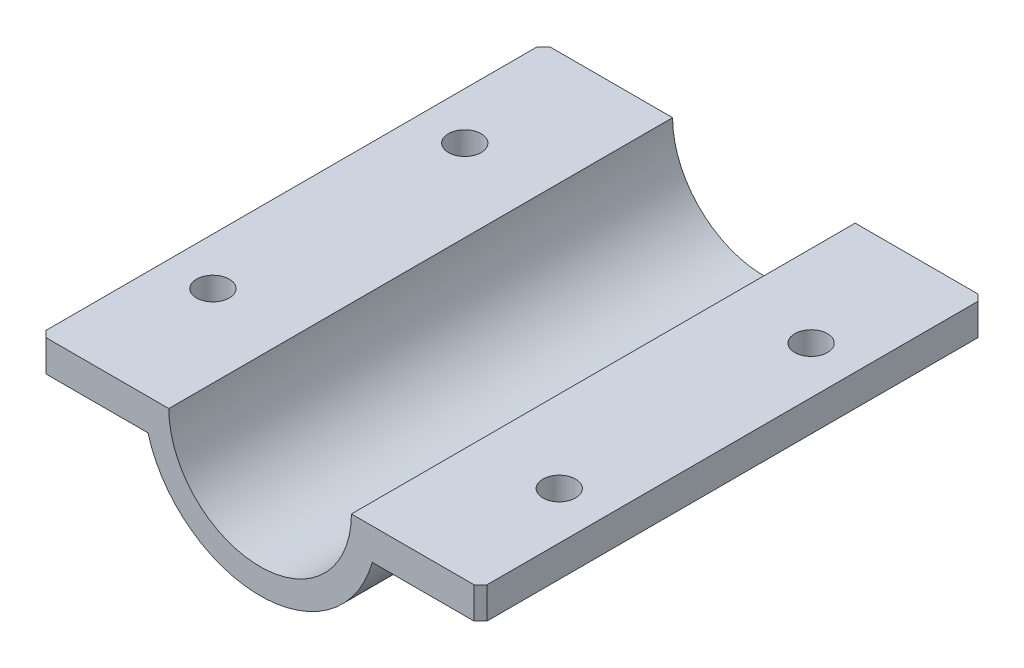
SolidWorks part; units mm, degrees
ref_plane "前视基准面" through (0, 0, 0) normal (0, 0, 1) x (1, 0, 0)
ref_plane "上视基准面" through (0, 0, 0) normal (0, 1, 0) x (1, 0, 0)
ref_plane "右视基准面" through (0, 0, 0) normal (1, 0, 0) x (0, 0, -1)
sketch "草图1" plane through (0, 0, 0) normal (0, 0, 1) x (1, 0, 0)
  line L0 (0, -14.5) -> (0, -22.5) construction
  line L1 (0, -22.5) -> (35, -22.5) construction
  line L2 (35, -22.5) -> (35, 0) construction
  line L3 (35, 0) -> (14.5, 0)
  line L5 (-35, -22.5) -> (0, -22.5) construction
  line L6 (-14.5, 0) -> (-35, 0)
  line L7 (-35, 0) -> (-35, -22.5) construction
  line L8 (-35, 0) -> (-35, -5)
  line L9 (-35, -5) -> (-21.9374, -5)
  line L10 (35, -5) -> (21.9374, -5)
  line L11 (35, 0) -> (35, -5)
  line L12 (-21.9374, -5) -> (-17.8115, -5)
  line L13 (21.9374, -5) -> (17.8115, -5)
  arc A0 (-14.5, 0) -> (14.5, 0) centre (0, 0) ccw
  arc A2 (-17.8115, -5) -> (17.8115, -5) centre (0, 0) ccw
  arc A3 (18.5, 0) -> (-18.5, 0) centre (0, 0) ccw construction
  dimension "D1" = 5
  dimension "D4" = 14.5
  dimension "D5" = 37
  dimension "D2" = 35
extrude "凸台-拉伸1" add sketch "草图1" along normal mid plane 80
sketch "草图2" plane through (0, -5, 0) normal (0, -1, 0) x (-1, 0, 0)
  line L0 (35, -40) -> (35, -20) construction
  line L1 (35, -40) -> (35, 40) construction
  line L2 (35, -20) -> (27.5, -20) construction
  line L3 (0, 0) -> (0, -10) construction
  line L4 (0, 0) -> (10, 0) construction
  circle A0 centre (27.5, -20) radius 2.6
  circle A1 centre (27.5, 20) radius 2.6
  circle A2 centre (-27.5, -20) radius 2.6
  circle A3 centre (-27.5, 20) radius 2.6
extrude "切除-拉伸1" cut sketch "草图2" against normal blind 10
chamfer "倒角1" distance 1 angle 45 4 edges at (-35, -2.5, -40) (35, -2.5, -40) (35, -2.5, 40) (-35, -2.5, 40)
